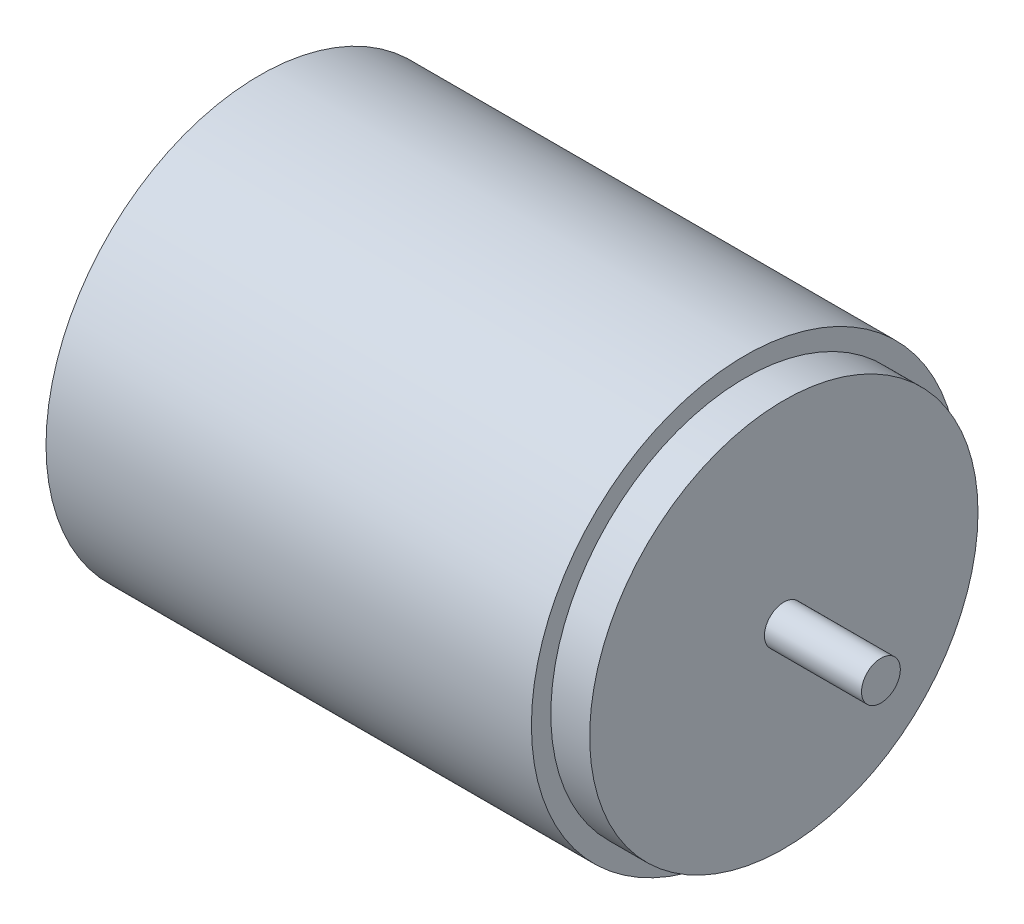
SolidWorks part; units mm, degrees
material "Stainless Steel (ferritic)"
ref_plane "Front Plane" through (0, 0, 0) normal (0, 0, 1) x (1, 0, 0)
ref_plane "Top Plane" through (0, 0, 0) normal (0, 1, 0) x (1, 0, 0)
ref_plane "Right Plane" through (0, 0, 0) normal (1, 0, 0) x (0, 0, -1)
sketch "Sketch1" plane through (0, 0, 0) normal (1, 0, 0) x (0, 0, -1)
  circle A0 centre (0, 0) radius 11
  dimension "D1" = 22
extrude "Boss-Extrude1" add sketch "Sketch1" along normal blind 25
sketch "Sketch2" plane through (25, 0, 0) normal (1, 0, 0) x (0, 0, -1)
  circle A0 centre (0, 0) radius 10
  dimension "D1" = 20
extrude "Boss-Extrude2" add sketch "Sketch2" along normal blind 2
sketch "Sketch3" plane through (27, 0, 0) normal (1, 0, 0) x (0, 0, -1)
  circle A0 centre (0, 0) radius 1
  dimension "D1" = 2
extrude "Boss-Extrude3" add sketch "Sketch3" along normal blind 5
